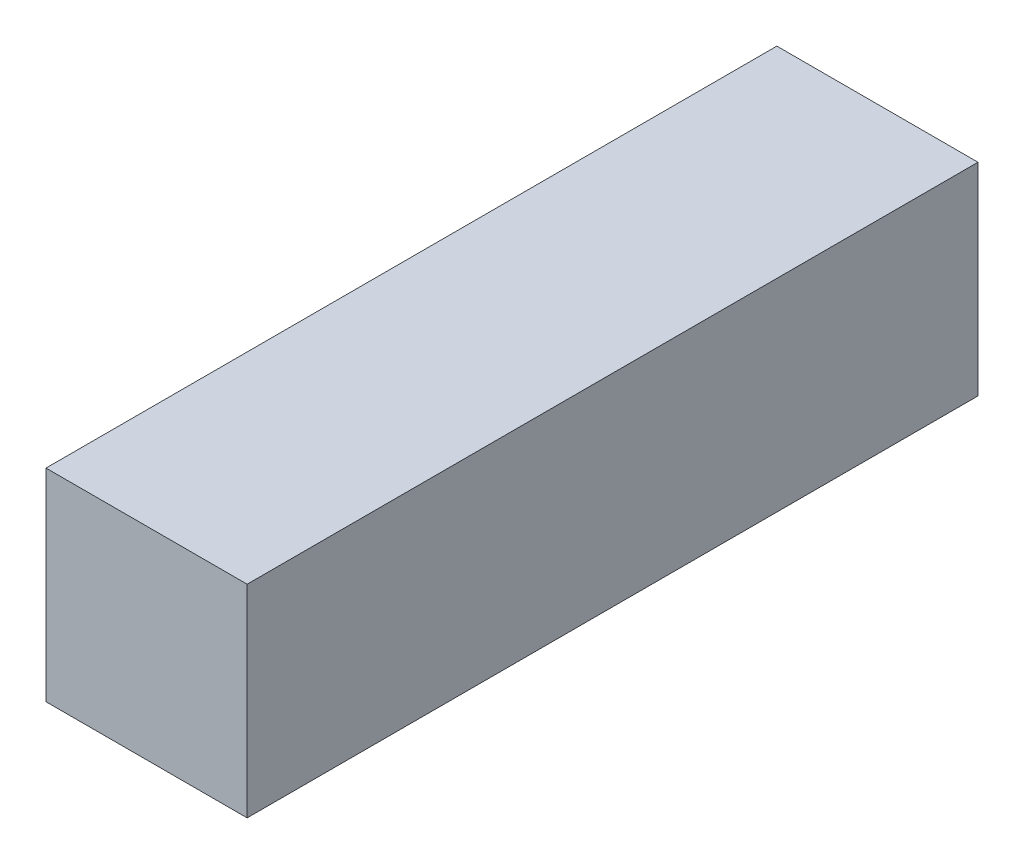
SolidWorks part; units mm, degrees
ref_plane "Front Plane" through (0, 0, 0) normal (0, 0, 1) x (1, 0, 0)
ref_plane "Top Plane" through (0, 0, 0) normal (0, 1, 0) x (1, 0, 0)
ref_plane "Right Plane" through (0, 0, 0) normal (1, 0, 0) x (0, 0, -1)
sketch "Sketch2" plane through (0, 0, 0) normal (0, 0, 1) x (1, 0, 0)
  line L1 (-16.1, -16.2) -> (16.1, -16.2)
  line L2 (-16.1, -16.2) -> (-16.1, 16.2)
  line L3 (-16.1, 16.2) -> (16.1, 16.2)
  line L4 (16.1, -16.2) -> (16.1, 16.2)
  line L5 (-16.1, -16.2) -> (16.1, 16.2) construction
  line L6 (-16.1, 16.2) -> (16.1, -16.2) construction
  point P0 (0, 0)
  dimension "D1" = 32.2
  dimension "D2" = 32.4
extrude "Boss-Extrude1" add sketch "Sketch2" along normal blind 117
